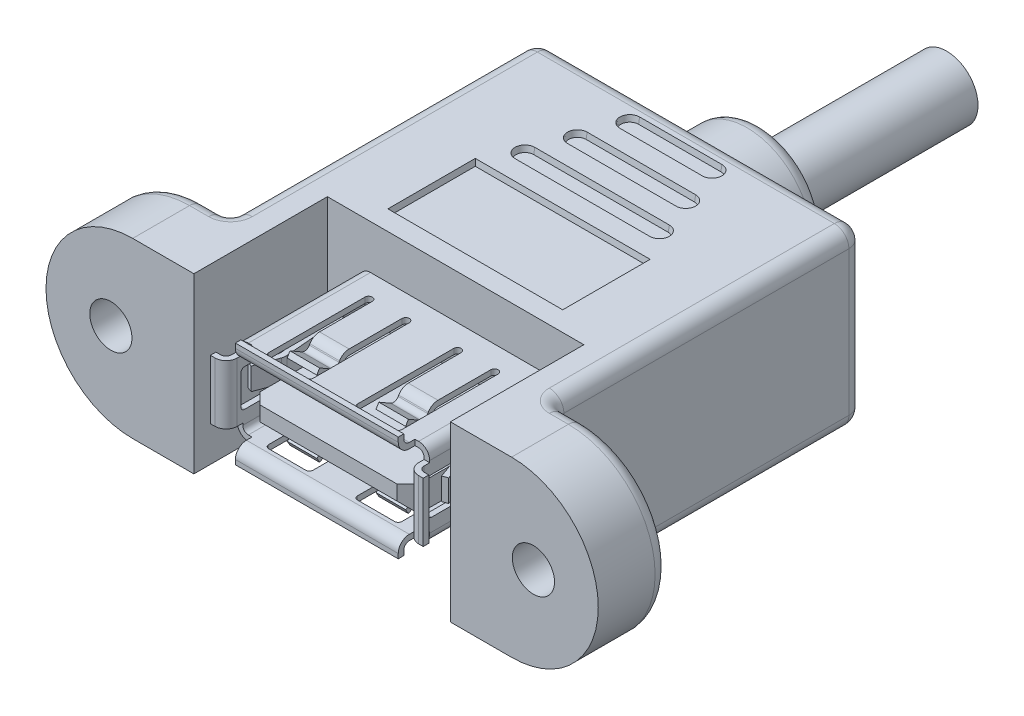
SolidWorks part; units mm, degrees
ref_plane "Front Plane" through (0, 0, 0) normal (0, 0, 1) x (1, 0, 0)
ref_plane "Top Plane" through (0, 0, 0) normal (0, 1, 0) x (1, 0, 0)
ref_plane "Right Plane" through (0, 0, 0) normal (1, 0, 0) x (0, 0, -1)
sketch "Sketch1" plane through (0, 0, 0) normal (0, 1, 0) x (1, 0, 0)
  line L0 (0, 0) -> (0, 57.7309) construction
  line L1 (-8.8, 0) -> (-8.8, -9.16)
  line L2 (-8.8, 0) -> (8.8, 0)
  line L3 (-11.19, -9.16) -> (-11.19, 15.8)
  line L4 (-10.19, 16.8) -> (10.19, 16.8)
  line L5 (11.19, -9.16) -> (11.19, 15.8)
  line L6 (8.8, 0) -> (8.8, -9.16)
  line L7 (-11.19, -9.16) -> (-8.8, -9.16)
  line L8 (8.8, -9.16) -> (11.19, -9.16)
  arc A0 (-11.19, 15.8) -> (-10.19, 16.8) centre (-10.19, 15.8) cw
  arc A1 (10.19, 16.8) -> (11.19, 15.8) centre (10.19, 15.8) cw
  point P3 (11.19, 17.9518)
  point P4 (-11.19, 17.9518)
  point P11 (-11.19, 15.24)
  point P12 (11.19, 15.24)
  dimension "D5" = 1
  dimension "D1" = 22.38
  dimension "D2" = 16.8
  dimension "D3" = 17.6
  dimension "D4" = 9.16
extrude "Extrude1" add sketch "Sketch1" along normal mid plane 11.9
sketch "Sketch3" plane through (0, 0, 9.16) normal (0, 0, 1) x (1, 0, 0)
  line L0 (-11.19, -5.95) -> (-8.8, -5.95) construction
  line L1 (8.8, 5.95) -> (13, 5.95)
  line L2 (8.8, 5.95) -> (8.8, -5.95)
  line L3 (8.8, -5.95) -> (13, -5.95)
  line L4 (0, 0) -> (-18.95, 0) construction
  line L5 (-8.8, 5.95) -> (-13, 5.95)
  line L6 (-8.8, 5.95) -> (-8.8, -5.95)
  line L7 (-8.8, -5.95) -> (-13, -5.95)
  line L8 (0, 0) -> (18.95, 0) construction
  line L9 (8.8, -5.95) -> (11.19, -5.95) construction
  arc A0 (-13, 5.95) -> (-13, -5.95) centre (-13, 0) ccw
  arc A1 (13, 5.95) -> (13, -5.95) centre (13, 0) cw
  point P14 (-18.95, 0)
  point P15 (18.95, 0)
  point P18 (19.4724, 0)
  dimension "D1" = 37.9
extrude "Extrude3" add sketch "Sketch3" against normal blind 4.9
sketch "Sketch5" plane through (0, 0, 9.16) normal (0, 0, 1) x (1, 0, 0)
  line L0 (0, 0) -> (0, 11.1761) construction
  line L1 (-7.2517, 3.4036) -> (7.2517, 3.4036) construction
  line L2 (-7.2517, 3.4036) -> (-7.2517, -3.4036) construction
  line L3 (-7.2517, -3.4036) -> (7.2517, -3.4036) construction
  line L4 (7.2517, 3.4036) -> (7.2517, -3.4036) construction
  line L5 (-14.5, 0) -> (14.5, 0) construction
  circle A0 centre (-14.5, 0) radius 1.4478
  circle A1 centre (14.5, 0) radius 1.4478
  point P8 (0, 3.4036)
  point P9 (0, 0)
  point P10 (0, 0)
  point P11 (0, 0)
  dimension "D3" = 2.8956
  dimension "D1" = 29
  dimension "D2" = 6.8072
  dimension "D5" = 14.5034
extrude "Cut-Extrude1" cut sketch "Sketch5" against normal up to surface (4.9 mm away) up to face at (-13.5825, 0, 4.26)
sketch "Sketch6" plane through (0, 0, 0) normal (0, 1, 0) x (1, 0, 0)
  line L0 (0, 27.38) -> (0, 9.0652) construction
  line L2 (0, 16.8) -> (4.45, 16.8)
  line L3 (0, 21) -> (4.45, 21)
  line L4 (4.45, 21) -> (4.45, 16.8)
  line L5 (0, 21) -> (0, 16.8)
  line L7 (10.19, 16.8) -> (-10.19, 16.8) construction
  point P2 (0, 16.8)
  point P3 (0, 16.8)
  point P9 (4.826, 16.8)
  point P10 (0, 0)
  point P12 (0, 0)
  point P14 (4.45, 16.8)
  dimension "D1" = 8.9
  dimension "D3" = 4.2
revolve "Revolve1" add sketch "Sketch6" angle 360
sketch "Sketch9" plane through (0, 0, -21) normal (0, 0, -1) x (-1, 0, 0)
  circle A0 centre (0, 0) radius 2.15
  dimension "D1" = 4.3
extrude "Extrude5" add sketch "Sketch9" along normal blind 12.7
sketch "Sketch7" plane through (0, -5.95, 0) normal (0, -1, 0) x (1, 0, 0)
  line L8 (-4.45, -16.8) -> (4.45, -16.8) construction
  line L10 (-4.6169, -9.375) -> (4.6169, -9.375) construction
  line L12 (-6, -1.35) -> (6, -1.35)
  line L13 (-6, -1.35) -> (-6, -7.35)
  line L14 (-6, -7.35) -> (6, -7.35)
  line L15 (6, -1.35) -> (6, -7.35)
  line L16 (-6, -1.35) -> (6, -7.35) construction
  line L17 (-6, -7.35) -> (6, -1.35) construction
  line L18 (-4.6169, -8.7) -> (4.6169, -8.7)
  line L19 (-4.6169, -10.05) -> (4.6169, -10.05)
  line L20 (-3.7209, -12.075) -> (3.7209, -12.075) construction
  line L21 (-3.7209, -11.4) -> (3.7209, -11.4)
  line L22 (-3.7209, -12.75) -> (3.7209, -12.75)
  line L23 (-2.825, -14.775) -> (2.825, -14.775) construction
  line L24 (-2.825, -14.1) -> (2.825, -14.1)
  line L25 (-2.825, -15.45) -> (2.825, -15.45)
  line L26 (0, 0) -> (0, -1.35) construction
  line L27 (0, -7.35) -> (0, -8.7) construction
  line L28 (0, -8.7) -> (0, -10.05) construction
  line L29 (0, -10.05) -> (0, -11.4) construction
  line L30 (0, -11.4) -> (0, -12.75) construction
  line L31 (0, -12.75) -> (0, -14.1) construction
  line L32 (0, -14.1) -> (0, -15.45) construction
  line L33 (0, -15.45) -> (0, -16.8) construction
  line L34 (6, -7.35) -> (3.4657, -14.9876) construction
  arc A8 (-4.6169, -8.7) -> (-4.6169, -10.05) centre (-4.6169, -9.375) ccw
  arc A9 (4.6169, -10.05) -> (4.6169, -8.7) centre (4.6169, -9.375) ccw
  arc A10 (-3.7209, -11.4) -> (-3.7209, -12.75) centre (-3.7209, -12.075) ccw
  arc A11 (3.7209, -12.75) -> (3.7209, -11.4) centre (3.7209, -12.075) ccw
  arc A12 (-2.825, -14.1) -> (-2.825, -15.45) centre (-2.825, -14.775) ccw
  arc A13 (2.825, -15.45) -> (2.825, -14.1) centre (2.825, -14.775) ccw
  point P4 (0, -4.35)
  point P11 (0, -9.375)
  point P17 (0, -12.075)
  point P24 (0, -14.775)
  point P34 (0, -9.7533)
  point P42 (3.5, -14.775)
  point P43 (-3.5, -14.775)
  dimension "D1" = 6
  dimension "D2" = 12
  dimension "D3" = 7
extrude "Cut-Extrude2" cut sketch "Sketch7" against normal blind 0.4 draft 10
sketch "Sketch8" plane through (0, 5.95, 0) normal (0, 1, 0) x (-1, 0, 0)
  line L2 (4.6169, -8.7) -> (-4.6169, -8.7)
  line L3 (-4.6169, -10.05) -> (4.6169, -10.05)
  line L4 (4.6169, -8.7) -> (-4.6169, -8.7)
  line L5 (-4.6169, -10.05) -> (4.6169, -10.05)
  line L6 (2.825, -14.1) -> (-2.825, -14.1)
  line L7 (-2.825, -15.45) -> (2.825, -15.45)
  line L8 (6, -1.35) -> (-6, -1.35)
  line L9 (-6, -1.35) -> (-6, -7.35)
  line L10 (-6, -7.35) -> (6, -7.35)
  line L11 (6, -7.35) -> (6, -1.35)
  line L12 (6, -1.35) -> (-6, -1.35)
  line L13 (-6, -1.35) -> (-6, -7.35)
  line L14 (-6, -7.35) -> (6, -7.35)
  line L15 (6, -7.35) -> (6, -1.35)
  line L16 (2.825, -14.1) -> (-2.825, -14.1)
  line L17 (-2.825, -15.45) -> (2.825, -15.45)
  line L18 (3.7209, -11.4) -> (-3.7209, -11.4)
  line L19 (-3.7209, -12.75) -> (3.7209, -12.75)
  line L20 (3.7209, -11.4) -> (-3.7209, -11.4)
  line L21 (-3.7209, -12.75) -> (3.7209, -12.75)
  arc A2 (-4.6169, -8.7) -> (-4.6169, -10.05) centre (-4.6169, -9.375) ccw
  arc A3 (4.6169, -10.05) -> (4.6169, -8.7) centre (4.6169, -9.375) ccw
  arc A4 (-4.6169, -8.7) -> (-4.6169, -10.05) centre (-4.6169, -9.375) ccw
  arc A5 (4.6169, -10.05) -> (4.6169, -8.7) centre (4.6169, -9.375) ccw
  arc A6 (-2.825, -14.1) -> (-2.825, -15.45) centre (-2.825, -14.775) ccw
  arc A7 (2.825, -15.45) -> (2.825, -14.1) centre (2.825, -14.775) ccw
  arc A8 (-2.825, -14.1) -> (-2.825, -15.45) centre (-2.825, -14.775) ccw
  arc A9 (2.825, -15.45) -> (2.825, -14.1) centre (2.825, -14.775) ccw
  arc A10 (-3.7209, -11.4) -> (-3.7209, -12.75) centre (-3.7209, -12.075) ccw
  arc A11 (3.7209, -12.75) -> (3.7209, -11.4) centre (3.7209, -12.075) ccw
  arc A12 (-3.7209, -11.4) -> (-3.7209, -12.75) centre (-3.7209, -12.075) ccw
  arc A13 (3.7209, -12.75) -> (3.7209, -11.4) centre (3.7209, -12.075) ccw
  dimension "D1" = 0
  dimension "D2" = 0
  dimension "D3" = 0
  dimension "D4" = 0
extrude "Cut-Extrude3" cut sketch "Sketch8" against normal blind 0.4 draft 10
fillet "Fillet1" radius 0.5 2 edges at (-11.19, 0, 4.26) (11.19, 0, 4.26)
sketch "Sketch10" plane through (0, 0, 0) normal (0, 0, 1) x (1, 0, 0)
  line L0 (-22.3107, 0) -> (0, 0) construction
  line L1 (0, 8.8149) -> (0, -8.8149) construction
  line L2 (-5.842, 2.54) -> (5.842, 2.54)
  line L3 (-5.842, 2.921) -> (5.842, 2.921)
  line L4 (-6.604, 2.159) -> (-6.604, -2.159)
  line L5 (-5.842, -2.921) -> (5.842, -2.921)
  line L6 (6.604, 2.159) -> (6.604, -2.159)
  line L7 (6.223, 2.159) -> (6.223, -2.159)
  line L8 (-5.842, -2.54) -> (5.842, -2.54)
  line L9 (-6.223, 2.159) -> (-6.223, -2.159)
  arc A0 (-6.604, 2.159) -> (-5.842, 2.921) centre (-5.842, 2.159) cw
  arc A1 (-5.842, -2.921) -> (-6.604, -2.159) centre (-5.842, -2.159) cw
  arc A2 (6.604, -2.159) -> (5.842, -2.921) centre (5.842, -2.159) cw
  arc A3 (5.842, 2.921) -> (6.604, 2.159) centre (5.842, 2.159) cw
  arc A4 (-6.223, 2.159) -> (-5.842, 2.54) centre (-5.842, 2.159) cw
  arc A5 (5.842, 2.54) -> (6.223, 2.159) centre (5.842, 2.159) cw
  arc A6 (6.223, -2.159) -> (5.842, -2.54) centre (5.842, -2.159) cw
  arc A7 (-5.842, -2.54) -> (-6.223, -2.159) centre (-5.842, -2.159) cw
  point P13 (-6.604, -2.921)
  point P16 (6.604, -2.921)
  dimension "D6" = 0.762
  dimension "D2" = 13.208
  dimension "D3" = 6.604
  dimension "D4" = 5.842
  dimension "D5" = 2.921
  dimension "D7" = 0.381
extrude "Extrude6" add sketch "Sketch10" along normal blind 8.382
sketch "Sketch11" plane through (0, 0, 8.382) normal (0, 0, 1) x (1, 0, 0)
  line L0 (-6.604, 2.159) -> (-6.604, -2.159) construction
  line L1 (-6.604, 2.032) -> (-6.223, 2.032)
  line L2 (-6.604, 2.032) -> (-6.604, -2.032)
  line L3 (-6.604, -2.032) -> (-6.223, -2.032)
  line L4 (-6.223, 2.032) -> (-6.223, -2.032)
  line L5 (-6.223, 2.159) -> (-6.223, -2.159) construction
  line L6 (-5.842, -2.54) -> (5.842, -2.54) construction
  line L7 (-5.588, -2.54) -> (5.588, -2.54)
  line L8 (-5.588, -2.54) -> (-5.588, -2.921)
  line L9 (-5.588, -2.921) -> (5.588, -2.921)
  line L10 (5.588, -2.54) -> (5.588, -2.921)
  line L11 (-5.842, -2.921) -> (5.842, -2.921) construction
  line L12 (5.842, 2.921) -> (-5.842, 2.921) construction
  line L13 (-5.588, 2.921) -> (5.588, 2.921)
  line L14 (-5.588, 2.921) -> (-5.588, 2.54)
  line L15 (-5.588, 2.54) -> (5.588, 2.54)
  line L16 (5.588, 2.921) -> (5.588, 2.54)
  line L17 (5.842, 2.54) -> (-5.842, 2.54) construction
  line L18 (6.223, -2.159) -> (6.223, 2.159) construction
  line L19 (6.223, 2.032) -> (6.604, 2.032)
  line L20 (6.223, 2.032) -> (6.223, -2.032)
  line L21 (6.223, -2.032) -> (6.604, -2.032)
  line L22 (6.604, 2.032) -> (6.604, -2.032)
  line L23 (6.604, -2.159) -> (6.604, 2.159) construction
  dimension "D1" = 11.176
  dimension "D2" = 4.064
  dimension "D3" = 0.889
  dimension "D4" = 1.016
extrude "Extrude7" add sketch "Sketch11" along normal blind 0.254
sketch "Sketch12" plane through (5.588, 0, 0) normal (1, 0, 0) x (0, 0, -1)
  line L0 (-9.525, 3.302) -> (-9.525, 3.6195)
  line L1 (-9.144, 3.302) -> (-9.144, 3.6195)
  line L2 (-9.525, 3.6195) -> (-9.144, 3.6195)
  line L3 (-9.525, -3.302) -> (-9.525, -3.6195)
  line L4 (-8.382, 2.54) -> (-8.382, 2.921)
  line L5 (-8.382, 2.921) -> (-8.636, 2.921)
  line L6 (-8.636, 2.921) -> (-8.636, 2.54)
  line L7 (-8.636, 2.54) -> (-8.382, 2.54)
  line L8 (-8.382, 2.54) -> (-8.382, 2.921)
  line L9 (-8.382, 2.921) -> (-8.763, 2.921)
  line L10 (-8.382, -2.921) -> (-8.382, -2.54)
  line L11 (-8.763, 2.54) -> (-8.382, 2.54)
  line L12 (-8.382, -2.54) -> (-8.636, -2.54)
  line L13 (-8.636, -2.54) -> (-8.636, -2.921)
  line L14 (-8.636, -2.921) -> (-8.382, -2.921)
  line L15 (-8.382, -2.921) -> (-8.382, -2.54)
  line L16 (-8.382, -2.54) -> (-8.763, -2.54)
  line L17 (-9.144, -3.302) -> (-9.144, -3.6195)
  line L18 (-8.763, -2.921) -> (-8.382, -2.921)
  line L19 (-9.525, -3.6195) -> (-9.144, -3.6195)
  line L20 (0, 0) -> (-11.5715, 0) construction
  line L25 (0, 5.95) -> (0, -5.95) construction
  arc A0 (-8.763, 2.54) -> (-9.525, 3.302) centre (-8.763, 3.302) cw
  arc A1 (-8.763, -2.54) -> (-9.525, -3.302) centre (-8.763, -3.302) ccw
  arc A2 (-8.763, 2.921) -> (-9.144, 3.302) centre (-8.763, 3.302) cw
  arc A3 (-8.763, -2.921) -> (-9.144, -3.302) centre (-8.763, -3.302) ccw
  dimension "D7" = 0.762
  dimension "D8" = 0.381
  dimension "D3" = 1.0795
  dimension "D4" = 1.0795
  dimension "D5" = 0.381
  dimension "D6" = 9.525
  dimension "D1" = 0
  dimension "D2" = 0
extrude "Extrude8" add sketch "Sketch12" against normal blind 11.176
sketch "Sketch13" plane through (0, 2.032, 0) normal (0, 1, 0) x (-1, 0, 0)
  line L0 (-6.985, 9.144) -> (-7.3025, 9.144)
  line L1 (-7.3025, 9.144) -> (-7.3025, 9.525)
  line L2 (-7.3025, 9.525) -> (-6.985, 9.525)
  line L3 (6.985, 9.144) -> (7.3025, 9.144)
  line L4 (6.223, 8.382) -> (6.604, 8.382)
  line L5 (6.604, 8.382) -> (6.604, 8.636)
  line L6 (6.604, 8.636) -> (6.223, 8.636)
  line L7 (6.223, 8.636) -> (6.223, 8.382)
  line L8 (6.223, 8.382) -> (6.604, 8.382)
  line L9 (6.604, 8.382) -> (6.604, 8.763)
  line L10 (7.3025, 9.144) -> (7.3025, 9.525)
  line L11 (6.223, 8.763) -> (6.223, 8.382)
  line L12 (-6.604, 8.382) -> (-6.223, 8.382)
  line L13 (-6.223, 8.382) -> (-6.223, 8.636)
  line L14 (-6.223, 8.636) -> (-6.604, 8.636)
  line L15 (-6.604, 8.636) -> (-6.604, 8.382)
  line L16 (-6.604, 8.382) -> (-6.223, 8.382)
  line L17 (-6.223, 8.382) -> (-6.223, 8.763)
  line L18 (7.3025, 9.525) -> (6.985, 9.525)
  line L19 (-6.604, 8.763) -> (-6.604, 8.382)
  line L20 (5.588, 9.525) -> (-5.588, 9.525) construction
  arc A0 (-6.985, 9.144) -> (-6.604, 8.763) centre (-6.985, 8.763) cw
  arc A1 (6.985, 9.144) -> (6.604, 8.763) centre (6.985, 8.763) ccw
  arc A2 (-6.223, 8.763) -> (-6.985, 9.525) centre (-6.985, 8.763) ccw
  arc A3 (6.985, 9.525) -> (6.223, 8.763) centre (6.985, 8.763) ccw
  point P26 (6.223, 9.525)
  dimension "D6" = 0.381
  dimension "D7" = 0.762
  dimension "D3" = 0.381
  dimension "D4" = 1.0795
  dimension "D5" = 1.0795
  dimension "D1" = 0
  dimension "D2" = 0
extrude "Extrude9" add sketch "Sketch13" against normal up to surface (4.064 mm away) up to face at (-6.4611, -2.032, 8.5725)
sketch "Sketch14" plane through (0, 2.921, 0) normal (0, 1, 0) x (-1, 0, 0)
  line L0 (0, 0) -> (0, 2.9776) construction
  line L1 (-2.032, 1.651) -> (-2.032, 2.159)
  line L2 (4.572, 1.651) -> (4.572, 8.255)
  line L3 (4.318, 8.509) -> (1.778, 8.509)
  line L4 (1.524, 1.651) -> (1.524, 8.255)
  line L5 (-3.048, 8.509) -> (-3.048, 0.7388) construction
  line L6 (-1.524, 1.651) -> (-1.524, 8.255)
  line L7 (-1.778, 8.509) -> (-4.318, 8.509)
  line L8 (-4.572, 1.651) -> (-4.572, 8.255)
  line L9 (-5.842, 0) -> (5.842, 0) construction
  line L10 (3.048, 8.509) -> (3.048, 0.7388) construction
  line L11 (-2.032, 2.159) -> (-4.064, 2.159)
  line L12 (5.588, 9.525) -> (-5.588, 9.525) construction
  line L13 (-4.064, 2.159) -> (-4.064, 1.651)
  line L14 (4.064, 1.651) -> (4.064, 2.159)
  line L15 (4.064, 2.159) -> (2.032, 2.159)
  line L16 (2.032, 2.159) -> (2.032, 1.651)
  arc A0 (-4.572, 8.255) -> (-4.318, 8.509) centre (-4.318, 8.255) cw
  arc A1 (-1.524, 8.255) -> (-1.778, 8.509) centre (-1.778, 8.255) ccw
  arc A2 (-2.032, 1.651) -> (-1.524, 1.651) centre (-1.778, 1.651) ccw
  arc A3 (-4.572, 1.651) -> (-4.064, 1.651) centre (-4.318, 1.651) ccw
  arc A4 (2.032, 1.651) -> (1.524, 1.651) centre (1.778, 1.651) cw
  arc A5 (4.572, 1.651) -> (4.064, 1.651) centre (4.318, 1.651) cw
  arc A6 (4.318, 8.509) -> (4.572, 8.255) centre (4.318, 8.255) cw
  arc A7 (1.524, 8.255) -> (1.778, 8.509) centre (1.778, 8.255) cw
  dimension "D6" = 7.112
  dimension "D1" = 0.254
  dimension "D7" = 0.762
  dimension "D2" = 1.016
  dimension "D3" = 3.048
  dimension "D4" = 6.096
  dimension "D5" = 3.048
extrude "Cut-Extrude4" cut sketch "Sketch14" against normal up to surface (5.842 mm away) up to face at (0, -2.921, 6.3818)
sketch "Sketch15" plane through (6.604, 0, 0) normal (1, 0, 0) x (0, 0, -1)
  line L0 (0, 0) -> (-4.7284, 0) construction
  line L1 (0, -2.159) -> (0, 2.159) construction
  line L2 (-9.525, -2.032) -> (-9.525, 2.032) construction
  line L3 (-8.255, 1.27) -> (-1.651, 1.27)
  line L4 (-8.509, 1.016) -> (-8.509, -1.016)
  line L5 (-8.255, -1.27) -> (-1.651, -1.27)
  line L6 (-1.651, 0.762) -> (-1.905, 0.762)
  line L7 (-1.905, 0.762) -> (-1.905, -0.762)
  line L8 (-1.905, -0.762) -> (-1.651, -0.762)
  arc A0 (-8.509, 1.016) -> (-8.255, 1.27) centre (-8.255, 1.016) cw
  arc A1 (-8.255, -1.27) -> (-8.509, -1.016) centre (-8.255, -1.016) cw
  arc A2 (-1.651, -0.762) -> (-1.651, -1.27) centre (-1.651, -1.016) cw
  arc A3 (-1.651, 1.27) -> (-1.651, 0.762) centre (-1.651, 1.016) cw
  point P12 (-8.509, 1.27)
  point P15 (-8.509, -1.27)
  dimension "D5" = 0.254
  dimension "D2" = 7.112
  dimension "D6" = 0.508
  dimension "D1" = 1.016
  dimension "D3" = 1.27
  dimension "D4" = 2.54
extrude "Cut-Extrude5" cut sketch "Sketch15" against normal blind 13.462
sketch "Sketch17" plane through (4.064, 0, 0) normal (1, 0, 0) x (0, 0, -1)
  line L0 (-5.935, 2.54) -> (-5.9716, 2.4765)
  line L1 (-8.509, 2.54) -> (-8.509, 2.921) construction
  line L2 (-6.4921, 2.337) -> (-7.3025, 2.8049)
  line L3 (-5.605, 2.3495) -> (-5.6417, 2.286)
  line L4 (-2.159, 2.54) -> (-1.651, 2.54)
  line L5 (-1.651, 2.54) -> (-1.651, 2.921)
  line L6 (-1.651, 2.921) -> (-2.159, 2.921)
  line L7 (-2.159, 2.921) -> (-2.159, 2.54)
  line L8 (-5.2751, 2.54) -> (-1.651, 2.54)
  line L9 (-1.651, 2.54) -> (-1.651, 2.921)
  line L10 (-1.651, 2.921) -> (-5.2751, 2.921)
  line L11 (-5.2751, 2.921) -> (-5.715, 2.921) construction
  line L12 (-6.6826, 2.0071) -> (-7.493, 2.475)
  line L13 (-7.493, 2.475) -> (-7.3025, 2.8049)
  line L14 (-5.715, 2.921) -> (-5.935, 2.54) construction
  line L15 (-5.6417, -2.286) -> (-5.605, -2.3495)
  line L16 (-6.6826, -2.0071) -> (-7.493, -2.475)
  line L17 (-5.935, -2.54) -> (-5.9716, -2.4765)
  line L18 (-6.4921, -2.337) -> (-7.3025, -2.8049)
  line L19 (-1.651, -2.54) -> (-2.159, -2.54)
  line L20 (-2.159, -2.54) -> (-2.159, -2.921)
  line L21 (-2.159, -2.921) -> (-1.651, -2.921)
  line L22 (-1.651, -2.921) -> (-1.651, -2.54)
  line L23 (-1.651, -2.54) -> (-5.2751, -2.54)
  line L24 (-7.493, -2.475) -> (-7.3025, -2.8049)
  line L25 (-5.2751, -2.921) -> (-1.651, -2.921)
  line L26 (-1.651, -2.921) -> (-1.651, -2.54)
  arc A0 (-6.4921, 2.337) -> (-5.9716, 2.4765) centre (-6.3016, 2.667) ccw
  arc A1 (-6.6826, 2.0071) -> (-5.6417, 2.286) centre (-6.3016, 2.667) ccw
  arc A2 (-5.2751, 2.921) -> (-5.935, 2.54) centre (-5.2751, 2.159) ccw
  arc A3 (-5.2751, 2.54) -> (-5.605, 2.3495) centre (-5.2751, 2.159) ccw
  arc A4 (-5.2751, -2.54) -> (-5.605, -2.3495) centre (-5.2751, -2.159) cw
  arc A5 (-5.9716, -2.4765) -> (-6.4921, -2.337) centre (-6.3016, -2.667) ccw
  arc A6 (-5.2751, -2.921) -> (-5.935, -2.54) centre (-5.2751, -2.159) cw
  arc A7 (-6.6826, -2.0071) -> (-5.6417, -2.286) centre (-6.3016, -2.667) cw
  dimension "D3" = 0.762
  dimension "D7" = 0.762
  dimension "D8" = 0.381
  dimension "D9" = 4.064
  dimension "D12" = 0.381
  dimension "D13" = 0.762
  dimension "D16" = 1.016
  dimension "D2" = 0.381
  dimension "D4" = 60
  dimension "D5" = 1.016
  dimension "D6" = 1.016
  dimension "D10" = 90
  dimension "D14" = 0.381
  dimension "D15" = 0.381
  dimension "D17" = 60
  dimension "D18" = 90
  dimension "D1" = 0
  dimension "D11" = 0
extrude "Extrude10" add sketch "Sketch17" against normal blind 2.032
sketch "Sketch18" plane through (-2.032, 0, 0) normal (1, 0, 0) x (0, 0, -1)
  line L8 (-5.935, 2.54) -> (-5.9716, 2.4765)
  line L9 (-6.4921, 2.337) -> (-7.3025, 2.8049)
  line L10 (-7.3025, 2.8049) -> (-7.493, 2.475)
  line L11 (-7.493, 2.475) -> (-6.6826, 2.0071)
  line L12 (-5.6417, 2.286) -> (-5.605, 2.3495)
  line L13 (-5.2751, 2.54) -> (-1.651, 2.54)
  line L14 (-1.651, 2.54) -> (-1.651, 2.921)
  line L15 (-1.651, 2.921) -> (-5.2751, 2.921)
  line L16 (-5.935, 2.54) -> (-5.9716, 2.4765)
  line L17 (-6.4921, 2.337) -> (-7.3025, 2.8049)
  line L18 (-7.3025, 2.8049) -> (-7.493, 2.475)
  line L19 (-7.493, 2.475) -> (-6.6826, 2.0071)
  line L20 (-5.6417, 2.286) -> (-5.605, 2.3495)
  line L21 (-5.2751, 2.54) -> (-1.651, 2.54)
  line L22 (-1.651, 2.54) -> (-1.651, 2.921)
  line L23 (-1.651, 2.921) -> (-5.2751, 2.921)
  line L24 (-5.605, -2.3495) -> (-5.6417, -2.286)
  line L25 (-1.651, -2.54) -> (-5.2751, -2.54)
  line L26 (-1.651, -2.921) -> (-1.651, -2.54)
  line L27 (-5.2751, -2.921) -> (-1.651, -2.921)
  line L28 (-5.9716, -2.4765) -> (-5.935, -2.54)
  line L29 (-7.3025, -2.8049) -> (-6.4921, -2.337)
  line L30 (-7.493, -2.475) -> (-7.3025, -2.8049)
  line L31 (-6.6826, -2.0071) -> (-7.493, -2.475)
  line L32 (-5.605, -2.3495) -> (-5.6417, -2.286)
  line L33 (-1.651, -2.54) -> (-5.2751, -2.54)
  line L34 (-1.651, -2.921) -> (-1.651, -2.54)
  line L35 (-5.2751, -2.921) -> (-1.651, -2.921)
  line L36 (-5.9716, -2.4765) -> (-5.935, -2.54)
  line L37 (-7.3025, -2.8049) -> (-6.4921, -2.337)
  line L38 (-7.493, -2.475) -> (-7.3025, -2.8049)
  line L39 (-6.6826, -2.0071) -> (-7.493, -2.475)
  arc A4 (-6.4921, 2.337) -> (-5.9716, 2.4765) centre (-6.3016, 2.667) ccw
  arc A5 (-6.6826, 2.0071) -> (-5.6417, 2.286) centre (-6.3016, 2.667) ccw
  arc A6 (-5.2751, 2.54) -> (-5.605, 2.3495) centre (-5.2751, 2.159) ccw
  arc A7 (-5.2751, 2.921) -> (-5.935, 2.54) centre (-5.2751, 2.159) ccw
  arc A8 (-6.4921, 2.337) -> (-5.9716, 2.4765) centre (-6.3016, 2.667) ccw
  arc A9 (-6.6826, 2.0071) -> (-5.6417, 2.286) centre (-6.3016, 2.667) ccw
  arc A10 (-5.2751, 2.54) -> (-5.605, 2.3495) centre (-5.2751, 2.159) ccw
  arc A11 (-5.2751, 2.921) -> (-5.935, 2.54) centre (-5.2751, 2.159) ccw
  arc A12 (-5.605, -2.3495) -> (-5.2751, -2.54) centre (-5.2751, -2.159) ccw
  arc A13 (-5.935, -2.54) -> (-5.2751, -2.921) centre (-5.2751, -2.159) ccw
  arc A14 (-5.9716, -2.4765) -> (-6.4921, -2.337) centre (-6.3016, -2.667) ccw
  arc A15 (-5.6417, -2.286) -> (-6.6826, -2.0071) centre (-6.3016, -2.667) ccw
  arc A16 (-5.605, -2.3495) -> (-5.2751, -2.54) centre (-5.2751, -2.159) ccw
  arc A17 (-5.935, -2.54) -> (-5.2751, -2.921) centre (-5.2751, -2.159) ccw
  arc A18 (-5.9716, -2.4765) -> (-6.4921, -2.337) centre (-6.3016, -2.667) ccw
  arc A19 (-5.6417, -2.286) -> (-6.6826, -2.0071) centre (-6.3016, -2.667) ccw
  dimension "D1" = 0
  dimension "D2" = 0
extrude "Extrude11" add sketch "Sketch18" against normal blind 2.032
sketch "Sketch20" plane through (0, 0.762, 0) normal (0, 1, 0) x (-1, 0, 0)
  line L0 (-6.6011, 2.4461) -> (-6.318, 5.6818)
  line L1 (-6.3395, 5.8453) -> (-6.8918, 7.3627)
  line L2 (-6.223, 2.3964) -> (-5.9385, 5.6486)
  line L3 (-5.9815, 5.9756) -> (-6.5338, 7.493)
  line L4 (-6.223, 1.651) -> (-6.223, 1.905)
  line L5 (-6.223, 1.905) -> (-6.604, 1.905)
  line L6 (-6.604, 1.905) -> (-6.604, 1.651)
  line L7 (-6.604, 1.651) -> (-6.223, 1.651)
  line L8 (-6.223, 1.651) -> (-6.223, 2.3964)
  line L9 (-6.5338, 7.493) -> (-6.8918, 7.3627)
  line L10 (-6.604, 2.3797) -> (-6.604, 1.651)
  line L11 (-6.604, 1.651) -> (-6.223, 1.651)
  line L12 (-6.223, 8.509) -> (-6.604, 8.509) construction
  line L13 (6.6011, 2.4461) -> (6.318, 5.6818)
  line L14 (6.3395, 5.8453) -> (6.8918, 7.3627)
  line L15 (6.223, 2.3964) -> (5.9385, 5.6486)
  line L16 (5.9815, 5.9756) -> (6.5338, 7.493)
  line L17 (6.223, 1.905) -> (6.223, 1.651)
  line L18 (6.223, 1.651) -> (6.604, 1.651)
  line L19 (6.604, 1.651) -> (6.604, 1.905)
  line L20 (6.604, 1.905) -> (6.223, 1.905)
  line L21 (6.223, 2.3964) -> (6.223, 1.651)
  line L22 (6.223, 1.651) -> (6.604, 1.651)
  line L23 (6.604, 1.651) -> (6.604, 2.3797)
  line L24 (6.8918, 7.3627) -> (6.5338, 7.493)
  line L25 (6.604, 8.509) -> (6.223, 8.509) construction
  arc A0 (-6.3395, 5.8453) -> (-6.318, 5.6818) centre (-6.6976, 5.715) cw
  arc A1 (-5.9815, 5.9756) -> (-5.9385, 5.6486) centre (-6.6976, 5.715) cw
  arc A2 (5.9815, 5.9756) -> (5.9385, 5.6486) centre (6.6976, 5.715) ccw
  arc A3 (6.3395, 5.8453) -> (6.318, 5.6818) centre (6.6976, 5.715) ccw
  arc A4 (-6.6011, 2.4461) -> (-6.604, 2.3797) centre (-5.842, 2.3797) ccw
  arc A5 (6.6011, 2.4461) -> (6.604, 2.3797) centre (5.842, 2.3797) cw
  point P34 (-6.604, 2.413)
  point P37 (6.604, 2.413)
  dimension "D6" = 0.381
  dimension "D7" = 0.762
  dimension "D15" = 0.762
  dimension "D16" = 0.381
  dimension "D19" = 4.064
  dimension "D21" = 0.762
  dimension "D2" = 0.762
  dimension "D3" = 5
  dimension "D4" = 0.381
  dimension "D5" = 0.381
  dimension "D8" = 1.016
  dimension "D9" = 25
  dimension "D10" = 4.064
  dimension "D12" = 0.762
  dimension "D13" = 5
  dimension "D14" = 0.381
  dimension "D17" = 1.016
  dimension "D18" = 25
  dimension "D20" = 0.381
  dimension "D1" = 0
  dimension "D11" = 0
extrude "Extrude12" add sketch "Sketch20" against normal blind 1.524
sketch "Sketch21" plane through (0, 0, 0) normal (0, 0, 1) x (1, 0, 0)
  line L0 (-6.223, 2.159) -> (-6.223, -2.159) construction
  line L1 (-5.461, -1.778) -> (5.461, -1.778)
  line L2 (-5.461, -1.778) -> (-5.461, 0)
  line L3 (-5.461, 0) -> (5.461, 0)
  line L4 (5.461, -1.778) -> (5.461, 0)
  line L5 (6.223, -2.159) -> (6.223, 2.159) construction
  line L7 (-5.842, -2.54) -> (5.842, -2.54) construction
  dimension "D1" = 0.762
  dimension "D2" = 0.762
  dimension "D3" = 0.762
  dimension "D4" = 1.778
extrude "Extrude14" add sketch "Sketch21" along normal blind 8.7376
chamfer "Chamfer2" distance 0.762 angle 45 2 edges at (-5.461, -0.889, 8.7376) (0, -1.778, 8.7376)
fillet "Fillet2" radius 1 21 edges at (-12.345, 5.95, 4.26) (-11.3364, 5.95, 4.1136) (-11.3364, -5.95, 4.1136) (-11.19, -5.95, -6.02) (-11.19, 5.95, -6.02) (-10.8971, -5.95, -16.5071) (-10.8971, 5.95, -16.5071) (0, -5.95, -16.8) (0, 5.95, -16.8) (10.8971, -5.95, -16.5071) (10.8971, 5.95, -16.5071) (11.19, 5.95, -6.02) (11.19, -5.95, -6.02) (11.3364, 5.95, 4.1136) (11.3364, -5.95, 4.1136) (12.345, 5.95, 4.26) (18.95, 0, 4.26) (12.345, -5.95, 4.26) (-12.345, -5.95, 4.26) (-4.45, 0, -21) (-18.95, 0, 4.26)
